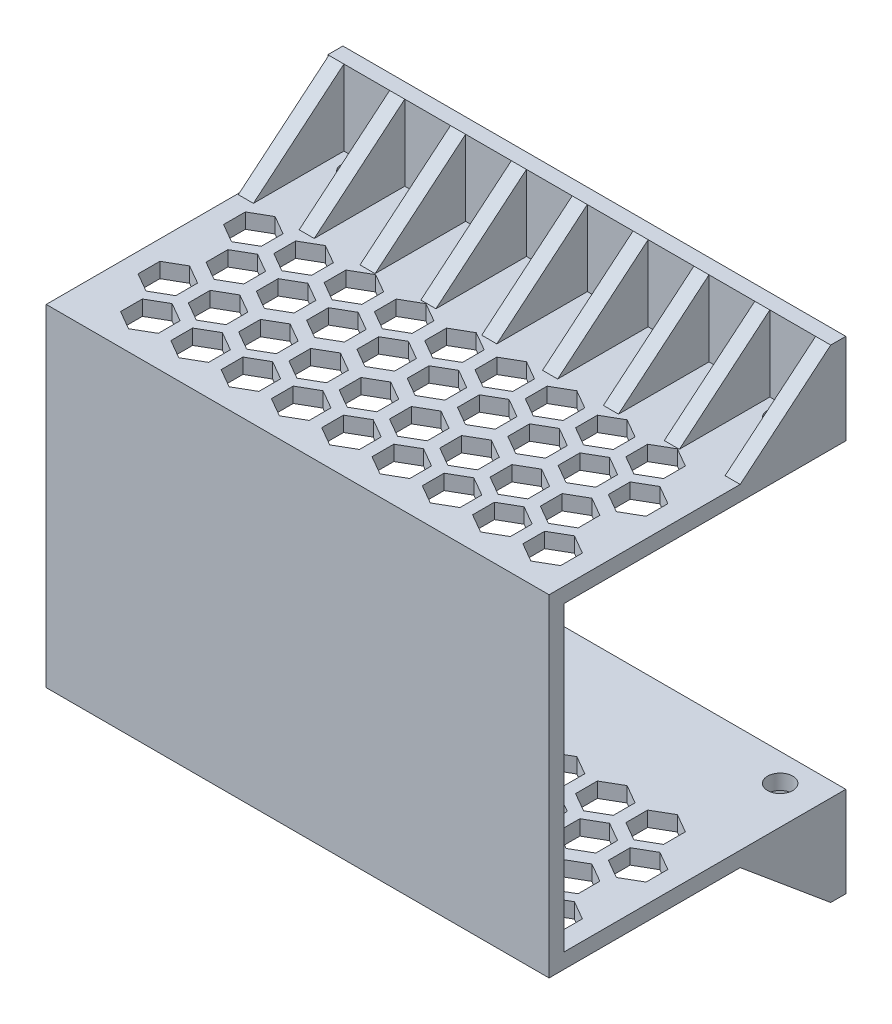
SolidWorks part; units mm, degrees
ref_plane "Front Plane" through (0, 0, 0) normal (0, 0, 1) x (1, 0, 0)
ref_plane "Top Plane" through (0, 0, 0) normal (0, 1, 0) x (1, 0, 0)
ref_plane "Right Plane" through (0, 0, 0) normal (1, 0, 0) x (0, 0, -1)
sketch "Sketch1" plane through (0, 0, 0) normal (0, 0, 1) x (1, 0, 0)
  line L0 (0, 0) -> (0, 60)
  line L1 (0, 60) -> (100, 60)
  line L2 (100, 60) -> (100, 0)
  line L3 (100, 0) -> (0, 0)
  dimension "D1" = 100
  dimension "D2" = 60
extrude "Boss-Extrude1" add sketch "Sketch1" along normal blind 3
sketch "Sketch2" plane through (0, 0, 0) normal (0, 0, -1) x (-1, 0, 0)
  line L0 (-100, 60) -> (0, 60) construction
  line L1 (-100, 60) -> (0, 60)
  line L2 (-100, 63) -> (0, 63)
  line L4 (0, 63) -> (0, 60)
  line L5 (0, -3) -> (-100, -3)
  line L6 (0, -3) -> (-100, -3)
  line L7 (-100, -3) -> (-100, 0)
  line L8 (0, -3) -> (0, 0)
  line L9 (-100, 63) -> (-100, 60)
  line M3 (-100, 0) -> (0, 0)
  line M5 (0, 60) -> (-100, 60)
  dimension "D1" = 3
  dimension "D2" = 3
extrude "Boss-Extrude2" add sketch "Sketch2" against normal blind 3 and the other way blind 53 contours L2 L9 L4 M5 | L6 L8 L7 M3
sketch "Sketch3" plane through (0, 0, -53) normal (0, 0, -1) x (-1, 0, 0)
  line L0 (0, 60) -> (-100, 60)
  line L1 (0, 60) -> (-100, 60) construction
  line L2 (-100, 60) -> (-100, 78)
  line L3 (-100, 78) -> (0, 78)
  line L4 (0, 78) -> (0, 60)
  line L5 (0, 30) -> (-100, 30) construction
  line L8 (0, 0) -> (-100, 0)
  line L9 (-100, 0) -> (-100, -18)
  line L10 (-100, -18) -> (0, -18)
  line L11 (0, -18) -> (0, 0)
  dimension "D1" = 18
extrude "Boss-Extrude3" add sketch "Sketch3" along normal blind 3
sketch "Sketch4" plane through (0, 63, 0) normal (0, 1, 0) x (1, 0, 0)
  line L216 (91.375, 11.3923) -> (91.375, 15.7224)
  line L217 (87.625, 9.2272) -> (91.375, 11.3923)
  line L218 (83.875, 11.3923) -> (87.625, 9.2272)
  line L219 (83.875, 15.7224) -> (83.875, 11.3923)
  line L220 (87.625, 17.8875) -> (83.875, 15.7224)
  line L221 (91.375, 15.7224) -> (87.625, 17.8875)
  line L222 (96.125, 7.4952) -> (92.375, 9.6603)
  line L223 (96.125, 3.1651) -> (96.125, 7.4952)
  line L224 (92.375, 1) -> (96.125, 3.1651)
  line L225 (88.625, 3.1651) -> (92.375, 1)
  line L226 (88.625, 7.4952) -> (88.625, 3.1651)
  line L227 (92.375, 9.6603) -> (88.625, 7.4952)
  line L236 (100, 53) -> (100, -3) construction
  line L238 (100, -3) -> (0, -3) construction
  line L239 (81.375, 11.3923) -> (81.375, 15.7224)
  line L240 (77.625, 9.2272) -> (81.375, 11.3923)
  line L241 (73.875, 11.3923) -> (77.625, 9.2272)
  line L242 (73.875, 15.7224) -> (73.875, 11.3923)
  line L243 (77.625, 17.8875) -> (73.875, 15.7224)
  line L244 (81.375, 15.7224) -> (77.625, 17.8875)
  line L245 (86.125, 7.4952) -> (82.375, 9.6603)
  line L246 (86.125, 3.1651) -> (86.125, 7.4952)
  line L247 (82.375, 1) -> (86.125, 3.1651)
  line L248 (78.625, 3.1651) -> (82.375, 1)
  line L249 (78.625, 7.4952) -> (78.625, 3.1651)
  line L250 (82.375, 9.6603) -> (78.625, 7.4952)
  line L251 (71.375, 11.3923) -> (71.375, 15.7224)
  line L252 (67.625, 9.2272) -> (71.375, 11.3923)
  line L253 (63.875, 11.3923) -> (67.625, 9.2272)
  line L254 (63.875, 15.7224) -> (63.875, 11.3923)
  line L255 (67.625, 17.8875) -> (63.875, 15.7224)
  line L256 (71.375, 15.7224) -> (67.625, 17.8875)
  line L257 (76.125, 7.4952) -> (72.375, 9.6603)
  line L258 (76.125, 3.1651) -> (76.125, 7.4952)
  line L259 (72.375, 1) -> (76.125, 3.1651)
  line L260 (68.625, 3.1651) -> (72.375, 1)
  line L261 (68.625, 7.4952) -> (68.625, 3.1651)
  line L262 (72.375, 9.6603) -> (68.625, 7.4952)
  line L263 (61.375, 11.3923) -> (61.375, 15.7224)
  line L264 (57.625, 9.2272) -> (61.375, 11.3923)
  line L265 (53.875, 11.3923) -> (57.625, 9.2272)
  line L266 (53.875, 15.7224) -> (53.875, 11.3923)
  line L267 (57.625, 17.8875) -> (53.875, 15.7224)
  line L268 (61.375, 15.7224) -> (57.625, 17.8875)
  line L269 (66.125, 7.4952) -> (62.375, 9.6603)
  line L270 (66.125, 3.1651) -> (66.125, 7.4952)
  line L271 (62.375, 1) -> (66.125, 3.1651)
  line L272 (58.625, 3.1651) -> (62.375, 1)
  line L273 (58.625, 7.4952) -> (58.625, 3.1651)
  line L274 (62.375, 9.6603) -> (58.625, 7.4952)
  line L275 (51.375, 11.3923) -> (51.375, 15.7224)
  line L276 (47.625, 9.2272) -> (51.375, 11.3923)
  line L277 (43.875, 11.3923) -> (47.625, 9.2272)
  line L278 (43.875, 15.7224) -> (43.875, 11.3923)
  line L279 (47.625, 17.8875) -> (43.875, 15.7224)
  line L280 (51.375, 15.7224) -> (47.625, 17.8875)
  line L281 (56.125, 7.4952) -> (52.375, 9.6603)
  line L282 (56.125, 3.1651) -> (56.125, 7.4952)
  line L283 (52.375, 1) -> (56.125, 3.1651)
  line L284 (48.625, 3.1651) -> (52.375, 1)
  line L285 (48.625, 7.4952) -> (48.625, 3.1651)
  line L286 (52.375, 9.6603) -> (48.625, 7.4952)
  line L287 (41.375, 11.3923) -> (41.375, 15.7224)
  line L288 (37.625, 9.2272) -> (41.375, 11.3923)
  line L289 (33.875, 11.3923) -> (37.625, 9.2272)
  line L290 (33.875, 15.7224) -> (33.875, 11.3923)
  line L291 (37.625, 17.8875) -> (33.875, 15.7224)
  line L292 (41.375, 15.7224) -> (37.625, 17.8875)
  line L293 (46.125, 7.4952) -> (42.375, 9.6603)
  line L294 (46.125, 3.1651) -> (46.125, 7.4952)
  line L295 (42.375, 1) -> (46.125, 3.1651)
  line L296 (38.625, 3.1651) -> (42.375, 1)
  line L297 (38.625, 7.4952) -> (38.625, 3.1651)
  line L298 (42.375, 9.6603) -> (38.625, 7.4952)
  line L299 (31.375, 11.3923) -> (31.375, 15.7224)
  line L300 (27.625, 9.2272) -> (31.375, 11.3923)
  line L301 (23.875, 11.3923) -> (27.625, 9.2272)
  line L302 (23.875, 15.7224) -> (23.875, 11.3923)
  line L303 (27.625, 17.8875) -> (23.875, 15.7224)
  line L304 (31.375, 15.7224) -> (27.625, 17.8875)
  line L305 (36.125, 7.4952) -> (32.375, 9.6603)
  line L306 (36.125, 3.1651) -> (36.125, 7.4952)
  line L307 (32.375, 1) -> (36.125, 3.1651)
  line L308 (28.625, 3.1651) -> (32.375, 1)
  line L309 (28.625, 7.4952) -> (28.625, 3.1651)
  line L310 (32.375, 9.6603) -> (28.625, 7.4952)
  line L311 (21.375, 11.3923) -> (21.375, 15.7224)
  line L312 (17.625, 9.2272) -> (21.375, 11.3923)
  line L313 (13.875, 11.3923) -> (17.625, 9.2272)
  line L314 (13.875, 15.7224) -> (13.875, 11.3923)
  line L315 (17.625, 17.8875) -> (13.875, 15.7224)
  line L316 (21.375, 15.7224) -> (17.625, 17.8875)
  line L317 (26.125, 7.4952) -> (22.375, 9.6603)
  line L318 (26.125, 3.1651) -> (26.125, 7.4952)
  line L319 (22.375, 1) -> (26.125, 3.1651)
  line L320 (18.625, 3.1651) -> (22.375, 1)
  line L321 (18.625, 7.4952) -> (18.625, 3.1651)
  line L322 (22.375, 9.6603) -> (18.625, 7.4952)
  line L323 (11.375, 11.3923) -> (11.375, 15.7224)
  line L324 (7.625, 9.2272) -> (11.375, 11.3923)
  line L325 (3.875, 11.3923) -> (7.625, 9.2272)
  line L326 (3.875, 15.7224) -> (3.875, 11.3923)
  line L327 (7.625, 17.8875) -> (3.875, 15.7224)
  line L328 (11.375, 15.7224) -> (7.625, 17.8875)
  line L329 (16.125, 7.4952) -> (12.375, 9.6603)
  line L330 (16.125, 3.1651) -> (16.125, 7.4952)
  line L331 (12.375, 1) -> (16.125, 3.1651)
  line L332 (8.625, 3.1651) -> (12.375, 1)
  line L333 (8.625, 7.4952) -> (8.625, 3.1651)
  line L334 (12.375, 9.6603) -> (8.625, 7.4952)
  line L335 (81.375, 28.3923) -> (81.375, 32.7224)
  line L336 (77.625, 26.2272) -> (81.375, 28.3923)
  line L337 (73.875, 28.3923) -> (77.625, 26.2272)
  line L338 (73.875, 32.7224) -> (73.875, 28.3923)
  line L339 (77.625, 34.8875) -> (73.875, 32.7224)
  line L340 (81.375, 32.7224) -> (77.625, 34.8875)
  line L341 (86.125, 24.4952) -> (82.375, 26.6603)
  line L342 (86.125, 20.1651) -> (86.125, 24.4952)
  line L343 (82.375, 18) -> (86.125, 20.1651)
  line L344 (78.625, 20.1651) -> (82.375, 18)
  line L345 (78.625, 24.4952) -> (78.625, 20.1651)
  line L346 (82.375, 26.6603) -> (78.625, 24.4952)
  line L347 (71.375, 28.3923) -> (71.375, 32.7224)
  line L348 (67.625, 26.2272) -> (71.375, 28.3923)
  line L349 (63.875, 28.3923) -> (67.625, 26.2272)
  line L350 (63.875, 32.7224) -> (63.875, 28.3923)
  line L351 (67.625, 34.8875) -> (63.875, 32.7224)
  line L352 (71.375, 32.7224) -> (67.625, 34.8875)
  line L353 (76.125, 24.4952) -> (72.375, 26.6603)
  line L354 (76.125, 20.1651) -> (76.125, 24.4952)
  line L355 (72.375, 18) -> (76.125, 20.1651)
  line L356 (68.625, 20.1651) -> (72.375, 18)
  line L357 (68.625, 24.4952) -> (68.625, 20.1651)
  line L358 (72.375, 26.6603) -> (68.625, 24.4952)
  line L359 (61.375, 28.3923) -> (61.375, 32.7224)
  line L360 (57.625, 26.2272) -> (61.375, 28.3923)
  line L361 (53.875, 28.3923) -> (57.625, 26.2272)
  line L362 (53.875, 32.7224) -> (53.875, 28.3923)
  line L363 (57.625, 34.8875) -> (53.875, 32.7224)
  line L364 (61.375, 32.7224) -> (57.625, 34.8875)
  line L365 (66.125, 24.4952) -> (62.375, 26.6603)
  line L366 (66.125, 20.1651) -> (66.125, 24.4952)
  line L367 (62.375, 18) -> (66.125, 20.1651)
  line L368 (58.625, 20.1651) -> (62.375, 18)
  line L369 (58.625, 24.4952) -> (58.625, 20.1651)
  line L370 (62.375, 26.6603) -> (58.625, 24.4952)
  line L371 (51.375, 28.3923) -> (51.375, 32.7224)
  line L372 (47.625, 26.2272) -> (51.375, 28.3923)
  line L373 (43.875, 28.3923) -> (47.625, 26.2272)
  line L374 (43.875, 32.7224) -> (43.875, 28.3923)
  line L375 (47.625, 34.8875) -> (43.875, 32.7224)
  line L376 (51.375, 32.7224) -> (47.625, 34.8875)
  line L377 (56.125, 24.4952) -> (52.375, 26.6603)
  line L378 (56.125, 20.1651) -> (56.125, 24.4952)
  line L379 (52.375, 18) -> (56.125, 20.1651)
  line L380 (48.625, 20.1651) -> (52.375, 18)
  line L381 (48.625, 24.4952) -> (48.625, 20.1651)
  line L382 (52.375, 26.6603) -> (48.625, 24.4952)
  line L383 (41.375, 28.3923) -> (41.375, 32.7224)
  line L384 (37.625, 26.2272) -> (41.375, 28.3923)
  line L385 (33.875, 28.3923) -> (37.625, 26.2272)
  line L386 (33.875, 32.7224) -> (33.875, 28.3923)
  line L387 (37.625, 34.8875) -> (33.875, 32.7224)
  line L388 (41.375, 32.7224) -> (37.625, 34.8875)
  line L389 (46.125, 24.4952) -> (42.375, 26.6603)
  line L390 (46.125, 20.1651) -> (46.125, 24.4952)
  line L391 (42.375, 18) -> (46.125, 20.1651)
  line L392 (38.625, 20.1651) -> (42.375, 18)
  line L393 (38.625, 24.4952) -> (38.625, 20.1651)
  line L394 (42.375, 26.6603) -> (38.625, 24.4952)
  line L395 (31.375, 28.3923) -> (31.375, 32.7224)
  line L396 (27.625, 26.2272) -> (31.375, 28.3923)
  line L397 (23.875, 28.3923) -> (27.625, 26.2272)
  line L398 (23.875, 32.7224) -> (23.875, 28.3923)
  line L399 (27.625, 34.8875) -> (23.875, 32.7224)
  line L400 (31.375, 32.7224) -> (27.625, 34.8875)
  line L401 (36.125, 24.4952) -> (32.375, 26.6603)
  line L402 (36.125, 20.1651) -> (36.125, 24.4952)
  line L403 (32.375, 18) -> (36.125, 20.1651)
  line L404 (28.625, 20.1651) -> (32.375, 18)
  line L405 (28.625, 24.4952) -> (28.625, 20.1651)
  line L406 (32.375, 26.6603) -> (28.625, 24.4952)
  line L407 (21.375, 28.3923) -> (21.375, 32.7224)
  line L408 (17.625, 26.2272) -> (21.375, 28.3923)
  line L409 (13.875, 28.3923) -> (17.625, 26.2272)
  line L410 (13.875, 32.7224) -> (13.875, 28.3923)
  line L411 (17.625, 34.8875) -> (13.875, 32.7224)
  line L412 (21.375, 32.7224) -> (17.625, 34.8875)
  line L413 (26.125, 24.4952) -> (22.375, 26.6603)
  line L414 (26.125, 20.1651) -> (26.125, 24.4952)
  line L415 (22.375, 18) -> (26.125, 20.1651)
  line L416 (18.625, 20.1651) -> (22.375, 18)
  line L417 (18.625, 24.4952) -> (18.625, 20.1651)
  line L418 (22.375, 26.6603) -> (18.625, 24.4952)
  line L419 (11.375, 28.3923) -> (11.375, 32.7224)
  line L420 (7.625, 26.2272) -> (11.375, 28.3923)
  line L421 (3.875, 28.3923) -> (7.625, 26.2272)
  line L422 (3.875, 32.7224) -> (3.875, 28.3923)
  line L423 (7.625, 34.8875) -> (3.875, 32.7224)
  line L424 (11.375, 32.7224) -> (7.625, 34.8875)
  line L425 (16.125, 24.4952) -> (12.375, 26.6603)
  line L426 (16.125, 20.1651) -> (16.125, 24.4952)
  line L427 (12.375, 18) -> (16.125, 20.1651)
  line L428 (8.625, 20.1651) -> (12.375, 18)
  line L429 (8.625, 24.4952) -> (8.625, 20.1651)
  line L430 (12.375, 26.6603) -> (8.625, 24.4952)
  line L431 (81.375, 45.3923) -> (81.375, 49.7224)
  line L432 (77.625, 43.2272) -> (81.375, 45.3923)
  line L433 (73.875, 45.3923) -> (77.625, 43.2272)
  line L434 (73.875, 49.7224) -> (73.875, 45.3923)
  line L435 (77.625, 51.8875) -> (73.875, 49.7224)
  line L436 (81.375, 49.7224) -> (77.625, 51.8875)
  line L437 (86.125, 41.4952) -> (82.375, 43.6603)
  line L438 (86.125, 37.1651) -> (86.125, 41.4952)
  line L439 (82.375, 35) -> (86.125, 37.1651)
  line L440 (78.625, 37.1651) -> (82.375, 35)
  line L441 (78.625, 41.4952) -> (78.625, 37.1651)
  line L442 (82.375, 43.6603) -> (78.625, 41.4952)
  line L443 (71.375, 45.3923) -> (71.375, 49.7224)
  line L444 (67.625, 43.2272) -> (71.375, 45.3923)
  line L445 (63.875, 45.3923) -> (67.625, 43.2272)
  line L446 (63.875, 49.7224) -> (63.875, 45.3923)
  line L447 (67.625, 51.8875) -> (63.875, 49.7224)
  line L448 (71.375, 49.7224) -> (67.625, 51.8875)
  line L449 (76.125, 41.4952) -> (72.375, 43.6603)
  line L450 (76.125, 37.1651) -> (76.125, 41.4952)
  line L451 (72.375, 35) -> (76.125, 37.1651)
  line L452 (68.625, 37.1651) -> (72.375, 35)
  line L453 (68.625, 41.4952) -> (68.625, 37.1651)
  line L454 (72.375, 43.6603) -> (68.625, 41.4952)
  line L455 (61.375, 45.3923) -> (61.375, 49.7224)
  line L456 (57.625, 43.2272) -> (61.375, 45.3923)
  line L457 (53.875, 45.3923) -> (57.625, 43.2272)
  line L458 (53.875, 49.7224) -> (53.875, 45.3923)
  line L459 (57.625, 51.8875) -> (53.875, 49.7224)
  line L460 (61.375, 49.7224) -> (57.625, 51.8875)
  line L461 (66.125, 41.4952) -> (62.375, 43.6603)
  line L462 (66.125, 37.1651) -> (66.125, 41.4952)
  line L463 (62.375, 35) -> (66.125, 37.1651)
  line L464 (58.625, 37.1651) -> (62.375, 35)
  line L465 (58.625, 41.4952) -> (58.625, 37.1651)
  line L466 (62.375, 43.6603) -> (58.625, 41.4952)
  line L467 (51.375, 45.3923) -> (51.375, 49.7224)
  line L468 (47.625, 43.2272) -> (51.375, 45.3923)
  line L469 (43.875, 45.3923) -> (47.625, 43.2272)
  line L470 (43.875, 49.7224) -> (43.875, 45.3923)
  line L471 (47.625, 51.8875) -> (43.875, 49.7224)
  line L472 (51.375, 49.7224) -> (47.625, 51.8875)
  line L473 (56.125, 41.4952) -> (52.375, 43.6603)
  line L474 (56.125, 37.1651) -> (56.125, 41.4952)
  line L475 (52.375, 35) -> (56.125, 37.1651)
  line L476 (48.625, 37.1651) -> (52.375, 35)
  line L477 (48.625, 41.4952) -> (48.625, 37.1651)
  line L478 (52.375, 43.6603) -> (48.625, 41.4952)
  line L479 (41.375, 45.3923) -> (41.375, 49.7224)
  line L480 (37.625, 43.2272) -> (41.375, 45.3923)
  line L481 (33.875, 45.3923) -> (37.625, 43.2272)
  line L482 (33.875, 49.7224) -> (33.875, 45.3923)
  line L483 (37.625, 51.8875) -> (33.875, 49.7224)
  line L484 (41.375, 49.7224) -> (37.625, 51.8875)
  line L485 (46.125, 41.4952) -> (42.375, 43.6603)
  line L486 (46.125, 37.1651) -> (46.125, 41.4952)
  line L487 (42.375, 35) -> (46.125, 37.1651)
  line L488 (38.625, 37.1651) -> (42.375, 35)
  line L489 (38.625, 41.4952) -> (38.625, 37.1651)
  line L490 (42.375, 43.6603) -> (38.625, 41.4952)
  line L491 (31.375, 45.3923) -> (31.375, 49.7224)
  line L492 (27.625, 43.2272) -> (31.375, 45.3923)
  line L493 (23.875, 45.3923) -> (27.625, 43.2272)
  line L494 (23.875, 49.7224) -> (23.875, 45.3923)
  line L495 (27.625, 51.8875) -> (23.875, 49.7224)
  line L496 (31.375, 49.7224) -> (27.625, 51.8875)
  line L497 (36.125, 41.4952) -> (32.375, 43.6603)
  line L498 (36.125, 37.1651) -> (36.125, 41.4952)
  line L499 (32.375, 35) -> (36.125, 37.1651)
  line L500 (28.625, 37.1651) -> (32.375, 35)
  line L501 (28.625, 41.4952) -> (28.625, 37.1651)
  line L502 (32.375, 43.6603) -> (28.625, 41.4952)
  line L503 (21.375, 45.3923) -> (21.375, 49.7224)
  line L504 (17.625, 43.2272) -> (21.375, 45.3923)
  line L505 (13.875, 45.3923) -> (17.625, 43.2272)
  line L506 (13.875, 49.7224) -> (13.875, 45.3923)
  line L507 (17.625, 51.8875) -> (13.875, 49.7224)
  line L508 (21.375, 49.7224) -> (17.625, 51.8875)
  line L509 (26.125, 41.4952) -> (22.375, 43.6603)
  line L510 (26.125, 37.1651) -> (26.125, 41.4952)
  line L511 (22.375, 35) -> (26.125, 37.1651)
  line L512 (18.625, 37.1651) -> (22.375, 35)
  line L513 (18.625, 41.4952) -> (18.625, 37.1651)
  line L514 (22.375, 43.6603) -> (18.625, 41.4952)
  line L515 (11.375, 45.3923) -> (11.375, 49.7224)
  line L516 (7.625, 43.2272) -> (11.375, 45.3923)
  line L517 (3.875, 45.3923) -> (7.625, 43.2272)
  line L518 (3.875, 49.7224) -> (3.875, 45.3923)
  line L519 (7.625, 51.8875) -> (3.875, 49.7224)
  line L520 (11.375, 49.7224) -> (7.625, 51.8875)
  line L521 (16.125, 41.4952) -> (12.375, 43.6603)
  line L522 (16.125, 37.1651) -> (16.125, 41.4952)
  line L523 (12.375, 35) -> (16.125, 37.1651)
  line L524 (8.625, 37.1651) -> (12.375, 35)
  line L525 (8.625, 41.4952) -> (8.625, 37.1651)
  line L526 (12.375, 43.6603) -> (8.625, 41.4952)
  line L527 (91.375, 28.3923) -> (91.375, 32.7224)
  line L528 (87.625, 26.2272) -> (91.375, 28.3923)
  line L529 (83.875, 28.3923) -> (87.625, 26.2272)
  line L530 (83.875, 32.7224) -> (83.875, 28.3923)
  line L531 (87.625, 34.8875) -> (83.875, 32.7224)
  line L532 (91.375, 32.7224) -> (87.625, 34.8875)
  line L533 (96.125, 24.4952) -> (92.375, 26.6603)
  line L534 (96.125, 20.1651) -> (96.125, 24.4952)
  line L535 (92.375, 18) -> (96.125, 20.1651)
  line L536 (88.625, 20.1651) -> (92.375, 18)
  line L537 (88.625, 24.4952) -> (88.625, 20.1651)
  line L538 (92.375, 26.6603) -> (88.625, 24.4952)
  line L539 (91.375, 45.3923) -> (91.375, 49.7224)
  line L540 (87.625, 43.2272) -> (91.375, 45.3923)
  line L541 (83.875, 45.3923) -> (87.625, 43.2272)
  line L542 (83.875, 49.7224) -> (83.875, 45.3923)
  line L543 (87.625, 51.8875) -> (83.875, 49.7224)
  line L544 (91.375, 49.7224) -> (87.625, 51.8875)
  line L545 (96.125, 41.4952) -> (92.375, 43.6603)
  line L546 (96.125, 37.1651) -> (96.125, 41.4952)
  line L547 (92.375, 35) -> (96.125, 37.1651)
  line L548 (88.625, 37.1651) -> (92.375, 35)
  line L549 (88.625, 41.4952) -> (88.625, 37.1651)
  line L550 (92.375, 43.6603) -> (88.625, 41.4952)
  circle A0 centre (92.375, 5.3301) radius 3.75 construction
  circle A1 centre (87.625, 13.5574) radius 3.75 construction
  dimension "D2" = 7.5
  dimension "D1" = 2
  dimension "D3" = 4.75
  dimension "D4" = 3.875
  dimension "D5" = 4
  dimension "D6" = 9
  dimension "D7" = 3
extrude "Cut-Extrude1" cut sketch "Sketch4" against normal through all
sketch "Sketch5" plane through (100, 0, 0) normal (1, 0, 0) x (0, 0, -1)
  line L0 (35, -3) -> (53, -3)
  line L1 (53, -3) -> (-3, -3) construction
  line L2 (53, -3) -> (53, -18)
  line L3 (53, -18) -> (35, -3)
  dimension "D1" = 18
extrude "Boss-Extrude4" add sketch "Sketch5" against normal blind 3
sketch "Sketch6" plane through (0, -3, 0) normal (0, -1, 0) x (1, 0, 0)
  line L0 (97, -35) -> (97, -53)
  line L1 (97, -53) -> (0, -53)
  line L2 (0, -53) -> (0, 3) construction
  line L3 (0, -53) -> (97, -53) construction
  line L4 (0, -53) -> (0, -35)
  line L5 (0, -35) -> (97, -35)
extrude "Boss-Extrude5" add sketch "Sketch6" against normal blind 3
pattern_linear "LPattern4" count 9 spacing 12.1 along (-1, 0, 0) of "Boss-Extrude4"
sketch "Sketch7" plane through (0, -3, 0) normal (0, -1, 0) x (1, 0, 0)
  line L0 (87.9, -53) -> (97, -53) construction
  line L1 (97, -53) -> (97, -35) construction
  line L3 (12.3, -53) -> (12.3, -35) construction
  line L4 (3.2, -53) -> (12.3, -53) construction
  circle A0 centre (92.45, -50.5) radius 2.5
  circle A1 centre (7.75, -50.5) radius 2.5
  dimension "D1" = 5
  dimension "D2" = 4.55
  dimension "D4" = 4.55
extrude "Cut-Extrude2" cut sketch "Sketch7" against normal through all
sketch "Sketch8" plane through (100, 0, 0) normal (1, 0, 0) x (0, 0, -1)
  line L0 (-3, 30) -> (61.5702, 30)
  line L1 (-3, -3) -> (-3, 63) construction
  line L2 (61.5702, 30) -> (61.5702, 89.777)
  line L3 (61.5702, 89.777) -> (-3, 89.777)
  line L4 (-3, 89.777) -> (-3, 30)
extrude "Cut-Extrude3" cut sketch "Sketch8" against normal through all
mirror "Mirror1" about plane through (0, 30, 3) normal (0, -1, 0) of bodies 109
